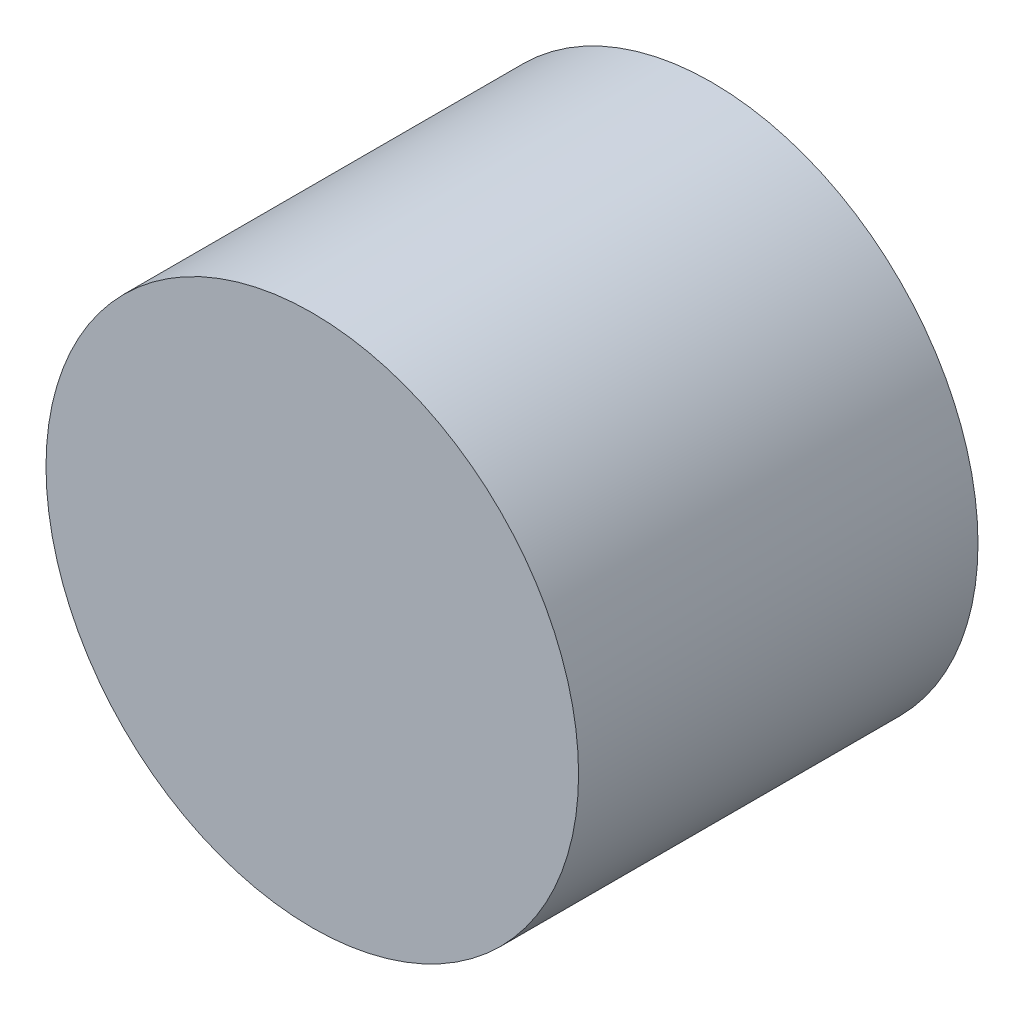
SolidWorks part; units mm, degrees
ref_plane "Front Plane" through (0, 0, 0) normal (0, 0, 1) x (1, 0, 0)
ref_plane "Top Plane" through (0, 0, 0) normal (0, 1, 0) x (1, 0, 0)
ref_plane "Right Plane" through (0, 0, 0) normal (1, 0, 0) x (0, 0, -1)
sketch "Sketch1" plane through (0, 0, 0) normal (0, 0, 1) x (1, 0, 0)
  circle A0 centre (0, -25.4) radius 12.7
  dimension "D1" = 25.4
extrude "Boss-Extrude1" add sketch "Sketch1" along normal blind 19.05
